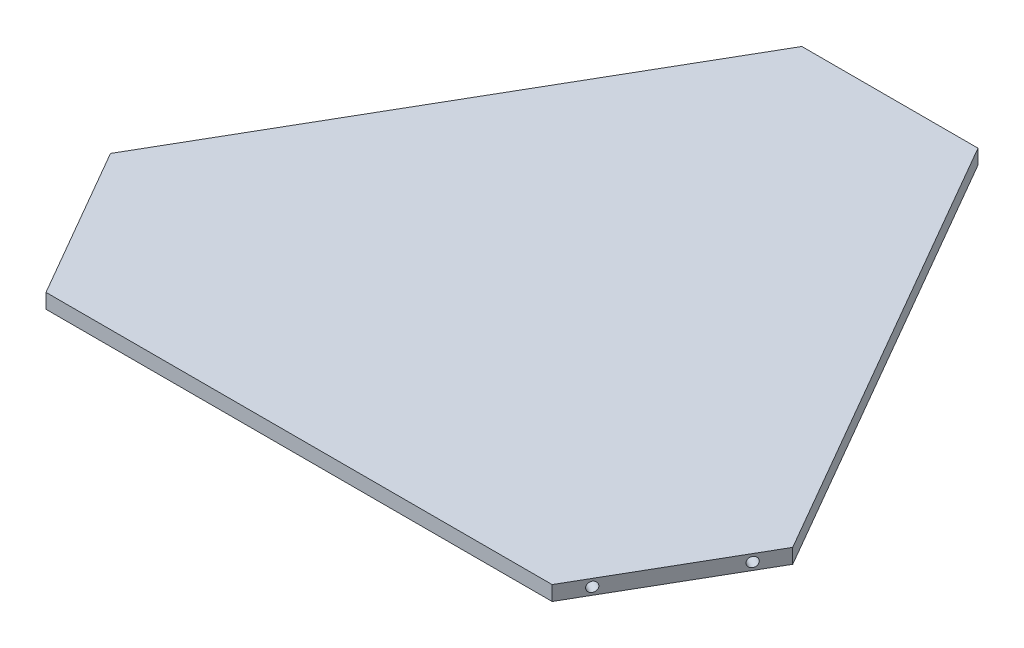
SolidWorks part; units mm, degrees
material "Acrylic (Medium-high impact)"
ref_plane "Front Plane" through (0, 0, 0) normal (0, 0, 1) x (1, 0, 0)
ref_plane "Top Plane" through (0, 0, 0) normal (0, 1, 0) x (1, 0, 0)
ref_plane "Right Plane" through (0, 0, 0) normal (1, 0, 0) x (0, 0, -1)
sketch "Sketch1" plane through (0, 0, 0) normal (0, 1, 0) x (1, 0, 0)
  line L0 (-147.591, -41.2176) -> (-109.491, -107.2088)
  line L1 (0, 214.4175) -> (-185.691, -107.2088) construction
  line L2 (-185.691, -107.2088) -> (185.691, -107.2088) construction
  line L3 (185.691, -107.2088) -> (0, 214.4175) construction
  line L4 (-109.491, -107.2088) -> (109.491, -107.2088)
  line L5 (109.491, -107.2088) -> (147.591, -41.2176)
  line L6 (147.591, -41.2176) -> (38.1, 148.4264)
  line L7 (38.1, 148.4264) -> (-38.1, 148.4264)
  line L8 (-38.1, 148.4264) -> (-147.591, -41.2176)
  circle A0 centre (0, 0) radius 107.2088 construction
  dimension "D1" = 120
  dimension "D2" = 120
  dimension "D3" = 148.4264
  dimension "D4" = 76.2
extrude "Boss-Extrude1" add sketch "Sketch1" along normal blind 6.35
hole_wizard "M5x0.8 Tapped Hole1" positions "Sketch2" profile "Sketch3" tap size "M5x0.8" standard "ANSI Metric"
sketch "Sketch2" plane through (128.541, 0, 74.2132) normal (0.866, 0, 0.5) x (0.5, 0, -0.866)
  line L0 (-25.4, 3.175) -> (25.4, 3.175) construction
  line L3 (38.1, 6.35) -> (38.1, 0) construction
  point P0 (-25.4, 3.175)
  point P2 (25.4, 3.175)
  point P10 (0, 3.175)
  point P15 (38.1, 3.175)
  dimension "D1" = 50.8
cosmetic thread "Hole Thread1" parameters "D1"=2.286, "D2"=5
cosmetic thread "Hole Thread2" parameters "D1"=2.286, "D2"=5
sketch "Sketch3" plane through (115.841, 3.175, 96.2102) normal (0, 1, 0) x (0.5, 0, -0.866)
  line L0 (0, 0) -> (0, 13.9618)
  line L1 (0, 13.9618) -> (2.1, 12.7)
  line L2 (2.1, 12.7) -> (2.1, 0)
  line L5 (2.1, 0) -> (0, 0)
  line L10 (0, 13.9618) -> (-2.1, 12.7) construction
  line L11 (0, -6.35) -> (0, 107.95) construction
  dimension "Tap Drill Dia." = 4.2
  dimension "Tap Drill Depth" = 12.7
  dimension "Drill Angle" = 118
ref_axis "Axis1" through (0, 6.6675, 0) along (0, -1, 0)
pattern_circular "CirPattern1" count 3 over 360 about axis through (0, 6.6675, 0) along (0, -1, 0) of "M5x0.8 Tapped Hole1"
